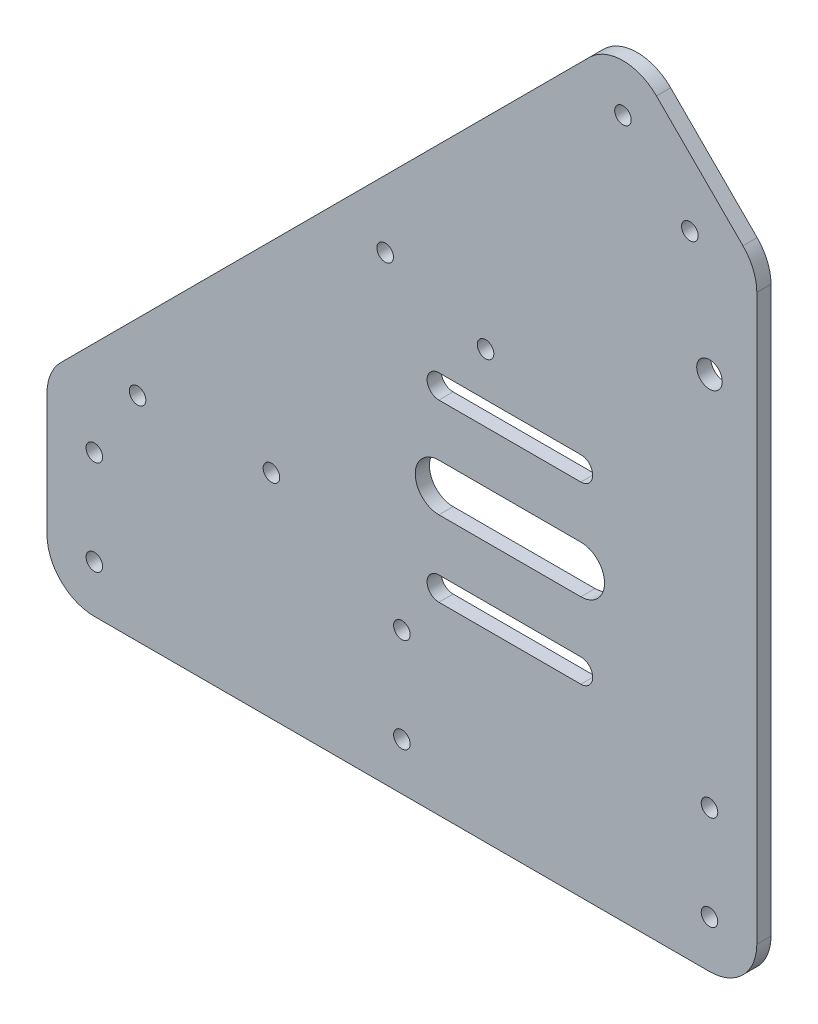
SolidWorks part; units mm, degrees
material "5052-H32"
ref_plane "Front Plane" through (0, 0, 0) normal (0, 0, 1) x (1, 0, 0)
ref_plane "Top Plane" through (0, 0, 0) normal (0, 1, 0) x (1, 0, 0)
ref_plane "Right Plane" through (0, 0, 0) normal (1, 0, 0) x (0, 0, -1)
sketch "Sketch1" plane through (0, 0, 0) normal (0, 0, 1) x (1, 0, 0)
  line L0 (-75, 20) -> (46.7157, 141.7157)
  line L1 (-18.4315, 20) -> (75, 20) construction
  line L2 (-75, 20) -> (-75, -20)
  line L3 (-75, -20) -> (75, -20)
  line L4 (75, 20) -> (75, -20)
  line L5 (-75, 20) -> (75, -20) construction
  line L6 (-75, -20) -> (75, 20) construction
  line L7 (-75, -20) -> (75, -20)
  line L11 (46.7157, 141.7157) -> (75, 113.4315)
  line L12 (75, 113.4315) -> (-18.4315, 20) construction
  line L13 (-75, 0) -> (75, 0) construction
  line L14 (-75, 10) -> (75, 10) construction
  line L15 (-75, -10) -> (75, -10) construction
  line L16 (60.8579, 127.5736) -> (-46.7157, 20) construction
  line L17 (-75, 20) -> (-18.4315, 20) construction
  line L18 (53.7868, 134.6447) -> (-60.8579, 20) construction
  line L19 (67.9289, 120.5025) -> (-32.5736, 20) construction
  line L20 (75, 113.4315) -> (75, 20)
  line L21 (46.7157, 127.5736) -> (60.8579, 113.4315) construction
  line L22 (65, -10) -> (65, 10) construction
  line L23 (-65, -10) -> (-65, 10) construction
  line L24 (7.8202, 40) -> (37.8202, 40) construction
  line L25 (7.8202, 45) -> (37.8202, 45)
  line L26 (7.8202, 35) -> (37.8202, 35)
  line L27 (65, 10) -> (65, 103.4315) construction
  line L28 (7.8202, 45) -> (7.8202, 58.5) construction
  line L29 (7.8202, 21.5) -> (37.8202, 21.5) construction
  line L30 (7.8202, 24) -> (37.8202, 24)
  line L31 (7.8202, 21.5) -> (7.8202, 35) construction
  line L32 (22.8202, 35) -> (22.8202, 45) construction
  line L33 (7.8202, 58.5) -> (37.8202, 58.5) construction
  line L34 (7.8202, 61) -> (37.8202, 61)
  line L35 (7.8202, 56) -> (37.8202, 56)
  line L36 (7.8202, 19) -> (37.8202, 19)
  line L38 (37.8202, 58.5) -> (37.8202, 21.5) construction
  line L42 (0, 20) -> (0, -20) construction
  line L43 (-10.6066, 84.3934) -> (17.6777, 56.1091) construction
  line L44 (24.7487, 63.1802) -> (-3.5355, 91.4645) construction
  line L45 (-55.8579, 25) -> (-62.9289, 32.0711) construction
  line L46 (-27.5736, 25) -> (-48.7868, 46.2132) construction
  line L47 (46.7157, 127.5736) -> (60.8579, 113.4315) construction
  line L48 (65, 89.2893) -> (75, 89.2893) construction
  line L49 (-65, -20) -> (-65, 20) construction
  circle A1 centre (22.8202, 40) radius 5 construction
  circle A2 centre (-65, -10) radius 1.75
  circle A3 centre (0, 10) radius 1.75
  circle A4 centre (65, -10) radius 1.75
  circle A5 centre (-55.8579, 25) radius 1.75
  circle A6 centre (46.7157, 127.5736) radius 1.75
  circle A8 centre (-27.5736, 25) radius 1.75
  circle A9 centre (60.8579, 113.4315) radius 1.75
  circle A10 centre (22.8202, 40) radius 4 construction
  circle A11 centre (-3.5355, 77.3223) radius 1.75
  circle A12 centre (17.6777, 70.2513) radius 1.75
  circle A13 centre (65, 10) radius 1.75
  circle A14 centre (-65, 10) radius 1.75
  circle A15 centre (0, -10) radius 1.75
  arc A16 (7.8202, 45) -> (7.8202, 35) centre (7.8202, 40) ccw
  arc A17 (37.8202, 35) -> (37.8202, 45) centre (37.8202, 40) ccw
  circle A18 centre (65, 89.2893) radius 2.7
  circle A19 centre (7.8202, 58.5) radius 2.5 construction
  circle A21 centre (7.8202, 21.5) radius 2.5 construction
  circle A22 centre (37.8202, 21.5) radius 2.5 construction
  circle A23 centre (37.8202, 58.5) radius 2.5 construction
  arc A26 (7.8202, 61) -> (7.8202, 56) centre (7.8202, 58.5) ccw
  arc A27 (37.8202, 56) -> (37.8202, 61) centre (37.8202, 58.5) ccw
  arc A28 (7.8202, 24) -> (7.8202, 19) centre (7.8202, 21.5) ccw
  arc A29 (37.8202, 19) -> (37.8202, 24) centre (37.8202, 21.5) ccw
  point P0 (0, 0)
  point P22 (-118.3455, 0)
  point P50 (22.8202, 40)
  point P63 (22.8202, 21.5)
  point P81 (22.8202, 58.5)
  dimension "D11" = 10
  dimension "D12" = 3.5
  dimension "D17" = 30
  dimension "D18" = 5.4
  dimension "D22" = 5
  dimension "D23" = 2.5
  dimension "D24" = 5
  dimension "D21" = 2.5
  dimension "D1" = 40
  dimension "D2" = 40
  dimension "D3" = 45
  dimension "D4" = 10
  dimension "D5" = 10
  dimension "D6" = 10
  dimension "D7" = 10
  dimension "D10" = 150
  dimension "D13" = 10
  dimension "D14" = 10
  dimension "D15" = 5
  dimension "D16" = 10
  dimension "D19" = 10
  dimension "D20" = 37
extrude "Boss-Extrude1" add sketch "Sketch1" along normal blind 3
fillet "Fillet1" radius 10 5 edges at (75, -20, 1.5) (-75, -20, 1.5) (46.7157, 141.7157, 1.5) (75, 113.4315, 1.5) (-75, 20, 1.5)
